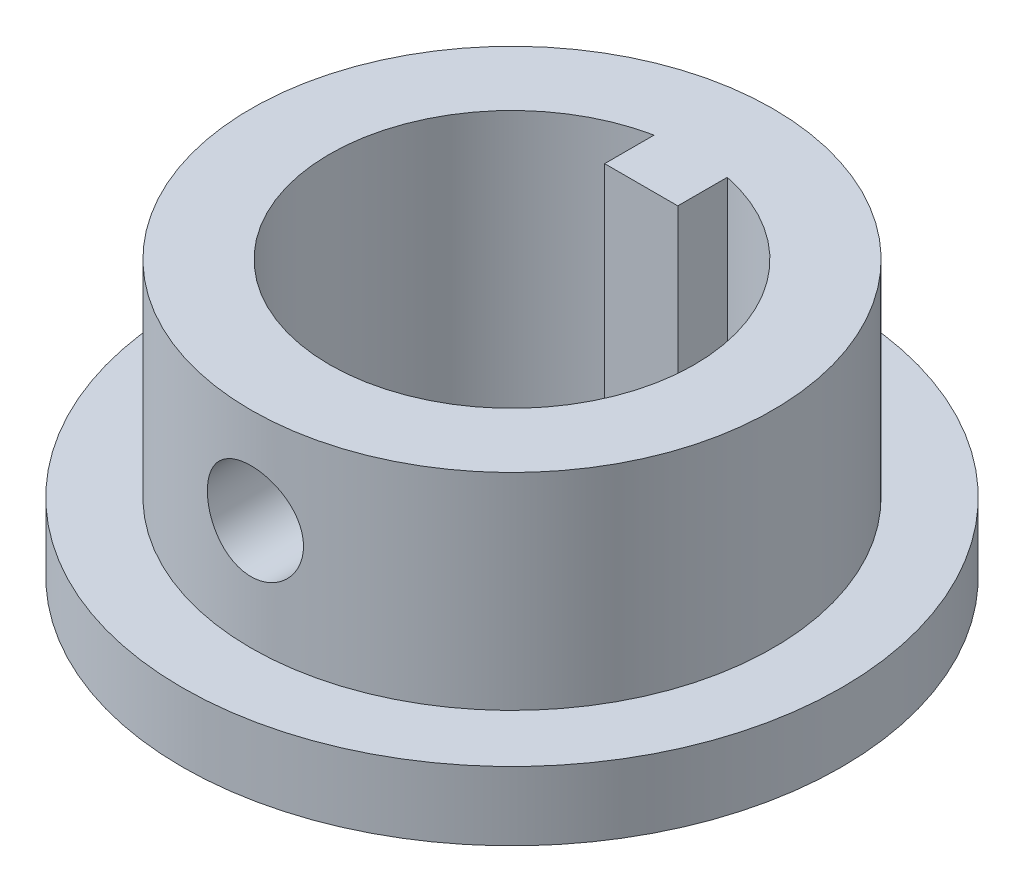
SolidWorks part; units mm, degrees
ref_plane "Front Plane" through (0, 0, 0) normal (0, 0, 1) x (1, 0, 0)
ref_plane "Top Plane" through (0, 0, 0) normal (0, 1, 0) x (1, 0, 0)
ref_plane "Right Plane" through (0, 0, 0) normal (1, 0, 0) x (0, 0, -1)
sketch "Sketch1" plane through (0, 0, 0) normal (0, 1, 0) x (1, 0, 0)
  line L0 (-1.332, 6.504) -> (-1.332, 4.704)
  line L1 (-1.332, 4.704) -> (1.33, 4.704)
  line L2 (1.33, 4.704) -> (1.33, 6.5044)
  circle A0 centre (0, 0) radius 9.5
  arc A1 (-1.332, 6.504) -> (1.33, 6.5044) centre (0, 0) ccw
  dimension "D1" = 13.278
  dimension "D2" = 19
  dimension "D3" = 1.8
  dimension "D4" = 2.662
  dimension "D5" = 1.33
extrude "Boss-Extrude1" add sketch "Sketch1" along normal blind 10
fillet "Fillet3" [suppressed] radius 1
sketch "Sketch2" plane through (0, 0, 0) normal (0, -1, 0) x (1, 0, 0)
  circle A0 centre (0, 0) radius 12
  circle A1 centre (0, 0) radius 9.5 construction
  dimension "D1" = 2.5
extrude "Boss-Extrude2" add sketch "Sketch2" against normal blind 2.5
sketch "Sketch4" plane through (0, 2.5, 0) normal (0, 1, 0) x (1, 0, 0)
  line L0 (-1.332, 4.704) -> (1.33, 4.704) construction
  line L1 (-1.332, 6.504) -> (-1.332, 4.704) construction
  line L2 (1.33, 4.704) -> (1.33, 6.5044) construction
  line L3 (-1.332, 4.704) -> (1.33, 4.704)
  line L4 (-1.332, 6.504) -> (-1.332, 4.704)
  line L5 (1.33, 4.704) -> (1.33, 6.5044)
  arc A0 (-1.332, 6.504) -> (1.33, 6.5044) centre (0, 0) ccw construction
  arc A1 (-1.332, 6.504) -> (1.33, 6.5044) centre (0, 0) ccw
extrude "Cut-Extrude2" cut sketch "Sketch4" against normal blind 2.5
sketch "Sketch5" plane through (0, 0, -4.704) normal (0, 0, 1) x (1, 0, 0)
  line L0 (1.33, 0) -> (-1.332, 0) construction
  circle A0 centre (-0.0001, 6.5) radius 1.75
  point P2 (-0.001, 0)
  dimension "D1" = 3.5
  dimension "D2" = 6.5
extrude "Cut-Extrude3" cut sketch "Sketch5" along normal blind 15
